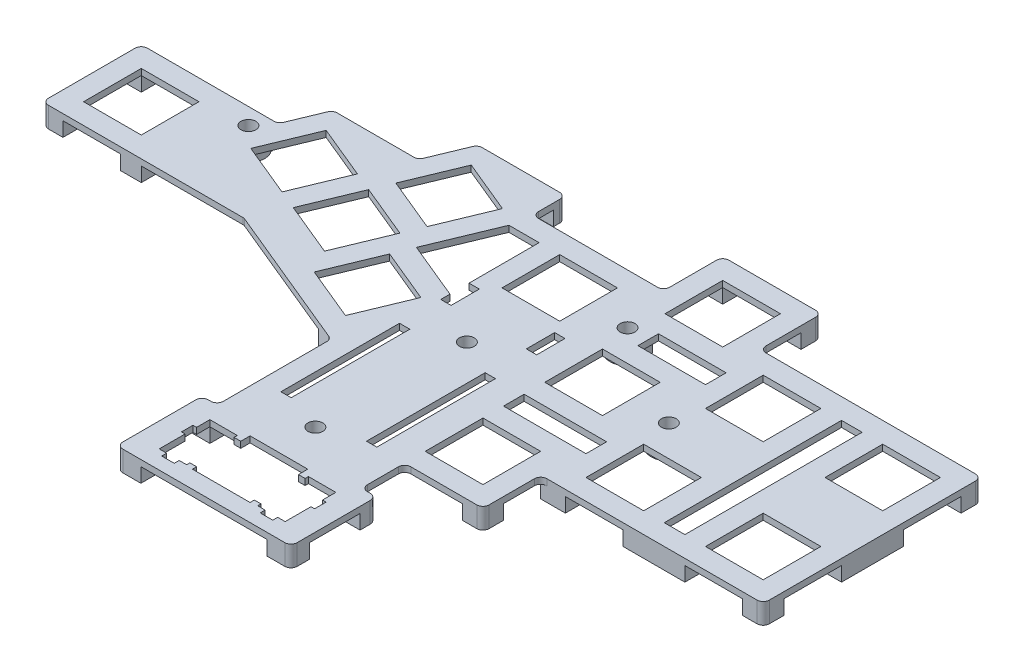
SolidWorks part; units mm, degrees
ref_plane "Front Plane" through (0, 0, 0) normal (0, 0, 1) x (1, 0, 0)
ref_plane "Top Plane" through (0, 0, 0) normal (0, 1, 0) x (1, 0, 0)
ref_plane "Right Plane" through (0, 0, 0) normal (1, 0, 0) x (0, 0, -1)
sketch "Button Reference" plane through (0, 0, 0) normal (0, 1, 0) x (1, 0, 0)
  line L0 (24.5, 61) -> (24.5, 32) construction
  line L1 (-36.2591, 48.1292) -> (-29.3708, 64.7591) construction
  line L2 (49.5, 75) -> (49.5, 46) construction
  line L3 (78.5, 75) -> (78.5, 46) construction
  line L4 (17.5, 0) -> (-17.5, 0) construction
  line L5 (-36.2591, 48.1292) -> (-19.6292, 41.2409) construction
  line L6 (17.5, -12.5) -> (-17.5, -12.5)
  line L7 (17.5, 12.5) -> (-17.5, 12.5)
  line L8 (24.6803, 89.9994) -> (49.5, 75) construction
  line L9 (24.6803, 89.9994) -> (24.5, 61) construction
  line L10 (-0.5241, 75.6559) -> (24.6803, 89.9994) construction
  line L11 (-0.5241, 75.6559) -> (24.5, 61) construction
  line L12 (-29.3708, 64.7591) -> (-12.7409, 57.8708) construction
  line L13 (-19.6292, 41.2409) -> (-12.7409, 57.8708) construction
  line L14 (-36.2591, 48.1292) -> (-12.7409, 57.8708) construction
  line L15 (-29.3708, 64.7591) -> (-19.6292, 41.2409) construction
  line L16 (-35.6984, 52.2266) -> (-28.8101, 68.8564) construction
  line L17 (-35.6984, 52.2266) -> (-52.3282, 59.1149) construction
  line L18 (-28.8101, 68.8564) -> (-45.4399, 75.7447) construction
  line L19 (-52.3282, 59.1149) -> (-45.4399, 75.7447) construction
  line L20 (-35.6984, 52.2266) -> (-45.4399, 75.7447) construction
  line L21 (-28.8101, 68.8564) -> (-52.3282, 59.1149) construction
  line L22 (-69.9281, 66.405) -> (-63.0398, 83.0348) construction
  line L23 (-69.9281, 66.405) -> (-53.2983, 59.5167) construction
  line L24 (-63.0398, 83.0348) -> (-46.41, 76.1465) construction
  line L25 (-53.2983, 59.5167) -> (-46.41, 76.1465) construction
  line L26 (-69.9281, 66.405) -> (-46.41, 76.1465) construction
  line L27 (-63.0398, 83.0348) -> (-53.2983, 59.5167) construction
  line L28 (-40.5692, 63.9856) -> (-22.9693, 56.6955) construction
  line L29 (-40.5692, 63.9856) -> (-58.1691, 71.2758) construction
  line L30 (-45.0381, 76.7148) -> (-38.1498, 93.3446) construction
  line L31 (-45.0381, 76.7148) -> (-28.4083, 69.8265) construction
  line L32 (-38.1498, 93.3446) -> (-21.52, 86.4563) construction
  line L33 (-28.4083, 69.8265) -> (-21.52, 86.4563) construction
  line L34 (-45.0381, 76.7148) -> (-21.52, 86.4563) construction
  line L35 (-38.1498, 93.3446) -> (-28.4083, 69.8265) construction
  line L36 (-40.5692, 63.9856) -> (-33.2791, 81.5855) construction
  line L37 (-24.5, 53) -> (-22.9693, 56.6955) construction
  line L38 (-58.1691, 71.2758) -> (-65.4592, 53.6759) construction
  line L39 (-65.4592, 53.6759) -> (-90.4039, 64.0083) construction
  line L40 (-70.5814, 66.1344) -> (-63.3104, 83.6881)
  line L41 (-63.3104, 83.6881) -> (-45.7105, 76.398)
  line L42 (-45.7105, 76.398) -> (-38.4204, 93.9979)
  line L43 (-38.4204, 93.9979) -> (-20.8667, 86.7269)
  line L44 (-20.8667, 86.7269) -> (-29.6876, 65.4315)
  line L45 (-29.6876, 65.4315) -> (-12.0877, 58.1414)
  line L46 (-12.0877, 58.1414) -> (-19.3586, 40.5877)
  line L47 (-19.3586, 40.5877) -> (-36.9123, 47.8586)
  line L48 (-36.9123, 47.8586) -> (-35.3816, 51.5542)
  line L49 (-35.3816, 51.5542) -> (-70.5814, 66.1344)
  line L50 (-66.484, 74.7199) -> (-66.9459, 74.9112) construction
  line L51 (-29.6436, 90.3624) -> (-29.8349, 89.9005) construction
  line L52 (-16.1851, 49.5558) -> (-15.7231, 49.3645) construction
  line L53 (-33.2791, 81.8539) -> (-33.2791, 81.5855) construction
  line L54 (46.566, 100.92) -> (46.566, 75) construction
  line L55 (46.566, 75) -> (49.5, 75) construction
  circle A0 centre (24.5, 32) radius 12.5
  circle A1 centre (24.5, 61) radius 12.5
  circle A2 centre (49.5, 46) radius 12.5
  circle A3 centre (49.5, 75) radius 12.5
  circle A4 centre (78.5, 75) radius 12.5
  circle A5 centre (78.5, 46) radius 12.5
  arc A6 (17.5, -12.5) -> (17.5, 12.5) centre (17.5, 0) ccw
  arc A7 (-17.5, 12.5) -> (-17.5, -12.5) centre (-17.5, 0) ccw
  circle A8 centre (-90.4039, 64.0083) radius 15.5
  circle A9 centre (24.6803, 89.9994) radius 12.5
  circle A10 centre (-0.5241, 75.6559) radius 12.5
  circle A11 centre (46.566, 100.92) radius 2.8
  circle A12 centre (62.066, 100.92) radius 2.8
  circle A13 centre (77.566, 100.92) radius 2.8
  circle A14 centre (93.066, 100.92) radius 2.8
  point P1 (-24.5, 53)
  point P3 (-40.5692, 63.9856)
  point P4 (-58.1691, 71.2758)
  point P35 (0, 0)
  point P43 (-33.2791, 81.5855)
  point P50 (-30, 0)
  point P51 (30, 0)
  dimension "D2" = 25
  dimension "D6" = 12.5
  dimension "D10" = 31
  dimension "D26" = 5.6
  dimension "D1" = 29
  dimension "D3" = 25
  dimension "D4" = 29
  dimension "D5" = 14
  dimension "D7" = 32
  dimension "D8" = 7
  dimension "D9" = 60
  dimension "D11" = 29
  dimension "D12" = 29
  dimension "D13" = 7
  dimension "D14" = 18
  dimension "D15" = 27
  dimension "D16" = 19.05
  dimension "D17" = 19.05
  dimension "D18" = 53
  dimension "D19" = 4
  dimension "D20" = 0.5
  dimension "D21" = 0.5
  dimension "D22" = 0.5
  dimension "D23" = 0.5
  dimension "D24" = 0.5
  dimension "D25" = 22.5
  dimension "D27" = 15.5
  dimension "D28" = 15.5
  dimension "D29" = 15.5
  dimension "D30" = 25.92
  dimension "D31" = 2.934
sketch "Sketch2" plane through (0, 0, 0) normal (0, 1, 0) x (1, 0, 0)
  line L0 (90.5, 34) -> (90.5, 87)
  line L1 (-97.4039, 57.0083) -> (-83.4039, 57.0083)
  line L2 (-97.4039, 57.0083) -> (-97.4039, 71.0083)
  line L3 (-97.4039, 71.0083) -> (-83.4039, 71.0083)
  line L4 (-83.4039, 57.0083) -> (-83.4039, 71.0083)
  line L5 (-97.4039, 57.0083) -> (-83.4039, 71.0083) construction
  line L6 (-97.4039, 71.0083) -> (-83.4039, 57.0083) construction
  line L11 (-67.315, 67.4874) -> (-61.9574, 80.4217)
  line L12 (-67.315, 67.4874) -> (-54.3807, 62.1298)
  line L17 (-61.9574, 80.4217) -> (-49.0231, 75.0641)
  line L18 (-54.3807, 62.1298) -> (-49.0231, 75.0641)
  line L23 (-67.315, 67.4874) -> (-49.0231, 75.0641) construction
  line L24 (-61.9574, 80.4217) -> (-54.3807, 62.1298) construction
  line L30 (-31.4232, 67.774) -> (-44.3575, 73.1316)
  line L31 (-31.4232, 67.774) -> (-36.7808, 54.8397)
  line L33 (-7.5241, 68.6559) -> (6.4759, 68.6559)
  line L34 (-7.5241, 68.6559) -> (-7.5241, 82.6559)
  line L35 (-7.5241, 82.6559) -> (6.4759, 82.6559)
  line L36 (6.4759, 68.6559) -> (6.4759, 82.6559)
  line L37 (-7.5241, 68.6559) -> (6.4759, 82.6559) construction
  line L38 (-7.5241, 82.6559) -> (6.4759, 68.6559) construction
  line L39 (17.6803, 82.9994) -> (31.6803, 82.9994)
  line L40 (17.6803, 82.9994) -> (17.6803, 96.9994)
  line L41 (17.6803, 96.9994) -> (31.6803, 96.9994)
  line L42 (31.6803, 82.9994) -> (31.6803, 96.9994)
  line L43 (17.6803, 82.9994) -> (31.6803, 96.9994) construction
  line L44 (17.6803, 96.9994) -> (31.6803, 82.9994) construction
  line L45 (17.5, 68) -> (31.5, 68)
  line L46 (17.5, 68) -> (17.5, 54)
  line L47 (17.5, 54) -> (31.5, 54)
  line L48 (31.5, 68) -> (31.5, 54)
  line L49 (17.5, 68) -> (31.5, 54) construction
  line L50 (17.5, 54) -> (31.5, 68) construction
  line L51 (17.5, 39) -> (31.5, 39)
  line L52 (17.5, 39) -> (17.5, 25)
  line L53 (17.5, 25) -> (31.5, 25)
  line L54 (31.5, 39) -> (31.5, 25)
  line L55 (17.5, 39) -> (31.5, 25) construction
  line L56 (17.5, 25) -> (31.5, 39) construction
  line L57 (42.5, 39) -> (56.5, 39)
  line L58 (42.5, 39) -> (42.5, 53)
  line L59 (42.5, 53) -> (56.5, 53)
  line L60 (56.5, 39) -> (56.5, 53)
  line L61 (42.5, 39) -> (56.5, 53) construction
  line L62 (42.5, 53) -> (56.5, 39) construction
  line L63 (42.5, 82) -> (56.5, 82)
  line L64 (42.5, 82) -> (42.5, 68)
  line L65 (42.5, 68) -> (56.5, 68)
  line L66 (56.5, 82) -> (56.5, 68)
  line L67 (42.5, 82) -> (56.5, 68) construction
  line L68 (42.5, 68) -> (56.5, 82) construction
  line L69 (71.5, 68) -> (85.5, 68)
  line L70 (71.5, 68) -> (71.5, 82)
  line L71 (71.5, 82) -> (85.5, 82)
  line L72 (85.5, 68) -> (85.5, 82)
  line L73 (71.5, 68) -> (85.5, 82) construction
  line L74 (71.5, 82) -> (85.5, 68) construction
  line L75 (71.5, 39) -> (85.5, 39)
  line L76 (71.5, 39) -> (71.5, 53)
  line L77 (71.5, 53) -> (85.5, 53)
  line L78 (85.5, 39) -> (85.5, 53)
  line L79 (71.5, 39) -> (85.5, 53) construction
  line L80 (71.5, 53) -> (85.5, 39) construction
  line L85 (7, 4.73) -> (8.6226, 4.73)
  line L88 (-44.3575, 73.1316) -> (-49.7151, 60.1973)
  line L89 (-36.7808, 54.8397) -> (-49.7151, 60.1973)
  line L90 (-31.4232, 67.774) -> (-49.7151, 60.1973) construction
  line L91 (-44.3575, 73.1316) -> (-36.7808, 54.8397) construction
  line L92 (-33.6459, 49.2116) -> (-20.7116, 43.8541)
  line L93 (-33.6459, 49.2116) -> (-28.2884, 62.1459)
  line L94 (-20.7116, 43.8541) -> (-15.3541, 56.7884)
  line L95 (-28.2884, 62.1459) -> (-15.3541, 56.7884)
  line L96 (-33.6459, 49.2116) -> (-15.3541, 56.7884) construction
  line L97 (-20.7116, 43.8541) -> (-28.2884, 62.1459) construction
  line L98 (-42.425, 77.7972) -> (-37.0674, 90.7315)
  line L99 (-42.425, 77.7972) -> (-29.4907, 72.4396)
  line L100 (-37.0674, 90.7315) -> (-24.1331, 85.3739)
  line L101 (-29.4907, 72.4396) -> (-24.1331, 85.3739)
  line L102 (-42.425, 77.7972) -> (-24.1331, 85.3739) construction
  line L103 (-37.0674, 90.7315) -> (-29.4907, 72.4396) construction
  line L104 (-28.8101, 68.8564) -> (-45.4399, 75.7447) construction
  line L106 (90.5, 87) -> (36.6803, 87)
  line L107 (36.6803, 87) -> (36.6803, 101.9994)
  line L128 (21.1524, -11.22) -> (-21.1524, -11.22)
  line L129 (-102.4039, 76.0083) -> (-102.4039, 52.0083)
  line L131 (90.5, 34) -> (36.5, 34)
  line L132 (36.5, 34) -> (36.5, 20)
  line L133 (36.5, 20) -> (17.5, 20)
  line L134 (17.5, 20) -> (17.5, 9.5)
  line L137 (36.6803, 101.9994) -> (12.6803, 101.9994)
  line L138 (-40.4083, 95.7315) -> (-44.6788, 85.4217)
  line L139 (-44.6788, 85.4217) -> (-65.2983, 85.4217)
  line L140 (-65.2983, 85.4217) -> (-69.1975, 76.0083)
  line L141 (-69.1975, 76.0083) -> (-102.4039, 76.0083)
  line L142 (-17.5, 9.5) -> (-17.5, 37.1118)
  line L143 (-17.5, 37.1118) -> (-53.4633, 52.0083)
  line L144 (-53.4633, 52.0083) -> (-102.4039, 52.0083)
  line L145 (-40.4083, 95.7315) -> (-19.1331, 95.7315)
  line L146 (12.6803, 87.6559) -> (12.6803, 101.9994)
  line L150 (-17.5, 9.5) -> (-21.1524, 9.5)
  line L151 (-21.1524, -11.22) -> (-21.1524, 9.5)
  line L154 (17.5, 9.5) -> (21.1524, 9.5)
  line L155 (21.1524, -11.22) -> (21.1524, 9.5)
  line L171 (-7, 7) -> (7, 7)
  line L174 (7, -7) -> (7, -5.97)
  line L175 (17.5, 9.5) -> (-17.5, 9.5) construction
  line L176 (0, 7) -> (0, -7) construction
  line L185 (-7, -7) -> (7, -7)
  line L186 (8.6226, 4.73) -> (8.6226, 5.53)
  line L187 (8.6226, 5.53) -> (15.2774, 5.53)
  line L188 (15.2774, 5.53) -> (15.2774, 2.3)
  line L189 (15.2774, 2.3) -> (16.1524, 2.3)
  line L190 (16.1524, 2.3) -> (16.1524, -0.5)
  line L191 (16.1524, -0.5) -> (15.2774, -0.5)
  line L192 (15.2774, -0.5) -> (15.2774, -6.77)
  line L193 (15.2774, -6.77) -> (13.474, -6.77)
  line L194 (13.474, -6.77) -> (13.474, -7.97)
  line L195 (13.474, -7.97) -> (10.426, -7.97)
  line L196 (10.426, -7.97) -> (10.426, -6.77)
  line L197 (10.426, -6.77) -> (8.6226, -6.77)
  line L198 (8.6226, -6.77) -> (8.6226, -5.97)
  line L199 (8.6226, -5.97) -> (7, -5.97)
  line L200 (11.95, 5.53) -> (11.95, -7.97) construction
  line L201 (-16.1524, 0) -> (16.1524, 0) construction
  line L202 (7, 4.73) -> (7, 7)
  line L203 (-8.6226, 4.73) -> (-8.6226, 5.53)
  line L204 (-8.6226, -6.77) -> (-8.6226, -5.97)
  line L205 (-7, -7) -> (-7, -5.97)
  line L206 (-8.6226, -5.97) -> (-7, -5.97)
  line L207 (-10.426, -6.77) -> (-8.6226, -6.77)
  line L208 (-10.426, -7.97) -> (-10.426, -6.77)
  line L209 (-13.474, -6.77) -> (-13.474, -7.97)
  line L210 (-13.474, -7.97) -> (-10.426, -7.97)
  line L211 (-11.95, 5.53) -> (-11.95, -7.97) construction
  line L212 (-15.2774, -6.77) -> (-13.474, -6.77)
  line L213 (-15.2774, -0.5) -> (-15.2774, -6.77)
  line L214 (-16.1524, -0.5) -> (-15.2774, -0.5)
  line L215 (-16.1524, 2.3) -> (-16.1524, -0.5)
  line L216 (-15.2774, 2.3) -> (-16.1524, 2.3)
  line L217 (-15.2774, 5.53) -> (-15.2774, 2.3)
  line L218 (-8.6226, 5.53) -> (-15.2774, 5.53)
  line L219 (-7, 4.73) -> (-8.6226, 4.73)
  line L220 (-7, 4.73) -> (-7, 7)
  line L222 (12.6803, 87.6559) -> (-19.1331, 87.6559)
  line L223 (-19.1331, 87.6559) -> (-19.1331, 95.7315)
  point P0 (-90.4039, 64.0083)
  point P6 (12.05, 5.1416)
  point P7 (-58.1691, 71.2758)
  point P8 (-40.5692, 63.9856)
  point P9 (-24.5, 53)
  point P15 (-33.2791, 81.5855)
  point P17 (0, 0)
  point P31 (-11.95, -7.97)
  point P32 (-0.5241, 75.6559)
  point P38 (24.6803, 89.9994)
  point P44 (24.5, 61)
  point P50 (24.5, 32)
  point P56 (49.5, 46)
  point P62 (49.5, 75)
  point P68 (78.5, 75)
  point P74 (78.5, 46)
  point P80 (0, 0)
  point P81 (0, 0)
  point P86 (0, 0)
  point P87 (0, 0)
  point P91 (0, 0)
  point P93 (0, 0)
  point P94 (12.6803, 99.1435)
  point P95 (0, 0)
  point P159 (0, 9.5)
  point P174 (0, 0)
  dimension "D2" = 5
  dimension "D3" = 14
  dimension "D5" = 5
  dimension "D6" = 5
  dimension "D7" = 5
  dimension "D8" = 5
  dimension "D9" = 5
  dimension "D10" = 6.6548
  dimension "D11" = 5
  dimension "D12" = 5
  dimension "D13" = 5
  dimension "D14" = 5
  dimension "D15" = 5
  dimension "D16" = 5
  dimension "D17" = 35
  dimension "D18" = 5
  dimension "D19" = 5
  dimension "D20" = 3.048
  dimension "D21" = 5
  dimension "D22" = 5
  dimension "D23" = 14
  dimension "D24" = 0.875
  dimension "D25" = 14
  dimension "D27" = 4.73
  dimension "D28" = 2.3
  dimension "D29" = 0.5
  dimension "D30" = 7.97
  dimension "D31" = 6.77
  dimension "D32" = 5.97
  dimension "D33" = 23.9
  dimension "D26" = 5.53
  dimension "D36" = 5
  dimension "D37" = 5
  dimension "D38" = 2.5
  dimension "D39" = 3.25
  dimension "D40" = 5
  dimension "D41" = 5
extrude "Key Plate" add sketch "Sketch2" along normal blind 1.5
sketch "Sketch3" plane through (0, 0, 0) normal (0, -1, 0) x (1, 0, 0)
  line L0 (-20.7116, -43.8541) -> (-22.625, -39.2347)
  line L13 (90.5, -34) -> (85.5, -34)
  line L14 (90.5, -34) -> (90.5, -39)
  line L15 (90.5, -39) -> (85.5, -39)
  line L16 (85.5, -34) -> (85.5, -39)
  line L17 (36.5, -20) -> (31.5, -20)
  line L18 (36.5, -20) -> (36.5, -25)
  line L19 (36.5, -25) -> (31.5, -25)
  line L20 (31.5, -20) -> (31.5, -25)
  line L29 (-102.4039, -52.0083) -> (-97.4039, -52.0083)
  line L30 (-102.4039, -52.0083) -> (-102.4039, -57.0083)
  line L31 (-102.4039, -57.0083) -> (-97.4039, -57.0083)
  line L32 (-97.4039, -52.0083) -> (-97.4039, -57.0083)
  line L33 (-97.4039, -71.0083) -> (-102.4039, -71.0083)
  line L34 (-97.4039, -71.0083) -> (-97.4039, -76.0083)
  line L35 (-97.4039, -76.0083) -> (-102.4039, -76.0083)
  line L36 (-102.4039, -71.0083) -> (-102.4039, -76.0083)
  line L37 (-20.7116, -43.8541) -> (-16.0922, -41.9406)
  line L38 (-22.625, -39.2347) -> (-18.0056, -37.3212)
  line L40 (-53.4633, -52.0083) -> (-17.5, -37.1118) construction
  line L49 (-16.0922, -41.9406) -> (-18.0056, -37.3212)
  line L51 (-102.4039, -52.0083) -> (-53.4633, -52.0083) construction
  line L52 (-83.4039, -57.0083) -> (-78.4039, -57.0083)
  line L53 (-83.4039, -57.0083) -> (-83.4039, -52.0083)
  line L54 (-83.4039, -52.0083) -> (-78.4039, -52.0083)
  line L55 (-78.4039, -57.0083) -> (-78.4039, -52.0083)
  line L56 (-38.4204, -93.9979) -> (-20.8667, -86.7269) construction
  line L57 (17.6803, -96.9994) -> (12.6803, -96.9994)
  line L58 (36.5, -34) -> (90.5, -34) construction
  line L59 (-83.4039, -71.0083) -> (-76.2052, -71.0083)
  line L60 (-83.4039, -71.0083) -> (-83.4039, -76.0083)
  line L61 (-83.4039, -76.0083) -> (-69.1975, -76.0083)
  line L62 (-69.1975, -74.2697) -> (-69.1975, -76.0083)
  line L71 (36.5, -34) -> (42.5, -34)
  line L72 (36.5, -34) -> (36.5, -39)
  line L73 (36.5, -39) -> (42.5, -39)
  line L74 (42.5, -34) -> (42.5, -39)
  line L75 (56.5, -39) -> (71.5, -39)
  line L76 (56.5, -39) -> (56.5, -34)
  line L77 (56.5, -34) -> (71.5, -34)
  line L78 (71.5, -39) -> (71.5, -34)
  line L79 (90.5, -34) -> (90.5, -87) construction
  line L80 (85.5, -53) -> (90.5, -53)
  line L81 (85.5, -53) -> (85.5, -68)
  line L82 (85.5, -68) -> (90.5, -68)
  line L83 (90.5, -53) -> (90.5, -68)
  line L85 (36.6803, -101.9994) -> (31.6803, -101.9994)
  line L86 (36.6803, -101.9994) -> (36.6803, -96.9994)
  line L87 (36.6803, -96.9994) -> (31.6803, -96.9994)
  line L88 (31.6803, -101.9994) -> (31.6803, -96.9994)
  line L89 (85.5, -82) -> (90.5, -82)
  line L90 (85.5, -82) -> (85.5, -87)
  line L91 (85.5, -87) -> (90.5, -87)
  line L92 (90.5, -82) -> (90.5, -87)
  line L95 (-70.5814, -66.1344) -> (-63.3104, -83.6881) construction
  line L96 (17.5, -12.5) -> (-17.5, -12.5) construction
  line L97 (17.6803, -96.9994) -> (17.6803, -101.9994)
  line L98 (17.6803, -101.9994) -> (12.6803, -101.9994)
  line L99 (12.6803, -96.9994) -> (12.6803, -101.9994)
  line L100 (-19.1331, -95.7315) -> (-35.363, -95.7315)
  line L101 (-19.1331, -95.7315) -> (-19.1331, -92.7315)
  line L102 (-19.1331, -92.7315) -> (-35.363, -92.7315)
  line L103 (-35.363, -95.7315) -> (-35.363, -92.7315)
  line L105 (21.1524, 11.22) -> (15.2774, 11.22)
  line L106 (21.1524, 11.22) -> (21.1524, 6.77)
  line L107 (21.1524, 6.77) -> (15.2774, 6.77)
  line L108 (15.2774, 11.22) -> (15.2774, 6.77)
  line L109 (-21.1524, 11.22) -> (-15.2774, 11.22)
  line L110 (-21.1524, 11.22) -> (-21.1524, 6.77)
  line L111 (-21.1524, 6.77) -> (-15.2774, 6.77)
  line L112 (-15.2774, 11.22) -> (-15.2774, 6.77)
  line L113 (21.1524, -9.5) -> (15.2774, -9.5)
  line L114 (21.1524, -9.5) -> (21.1524, -5.53)
  line L115 (21.1524, -5.53) -> (15.2774, -5.53)
  line L116 (15.2774, -9.5) -> (15.2774, -5.53)
  line L117 (-21.1524, -9.5) -> (-15.2774, -9.5)
  line L118 (-21.1524, -9.5) -> (-21.1524, -5.53)
  line L119 (-21.1524, -5.53) -> (-15.2774, -5.53)
  line L120 (-15.2774, -9.5) -> (-15.2774, -5.53)
  circle A0 centre (-0.4039, -53) radius 4.25
  circle A1 centre (-0.9039, -16.75) radius 4.25
  circle A2 centre (41.0961, -60.5) radius 4.2594
  circle A3 centre (16.0961, -75.5) radius 4.2594
  arc A4 (-69.1975, -74.2697) -> (-76.2052, -71.0083) centre (-72.4039, -72) ccw
  circle A5 centre (24.5, -61) radius 12.5 construction
  circle A6 centre (49.5, -46) radius 12.5 construction
  point P0 (41.0961, -60.5)
  dimension "D1" = 8.5
  dimension "D2" = 3
  dimension "D3" = 5
extrude "Feet" add sketch "Sketch3" along normal blind 3.5
hole_wizard "M3 Clearance Hole1" positions "3DSketch1" profile "Sketch5" hole size "M3" standard "ANSI Metric" end condition up to next
sketch3d "3DSketch1"
  line L0 (-0.4039, -3.5, -53) -> (-0.4039, 0, -53) construction
  line L1 (16.0961, -3.5, -75.5) -> (16.0961, 0, -75.5) construction
  line L2 (-0.9039, -3.5, -16.75) -> (-0.9039, 0, -16.75) construction
  line L3 (41.0961, -3.5, -60.5) -> (41.0961, 0, -60.5) construction
  line L4 (-72.4039, -3.5, -72) -> (-72.4039, 0, -72) construction
  point P0 (-0.4039, -3.5, -53)
  point P4 (41.0961, -3.5, -60.5)
  point P6 (16.0961, -3.5, -75.5)
  point P10 (-0.9039, -3.5, -16.75)
  point P18 (-72.4039, -3.5, -72)
sketch "Sketch5" plane through (-0.4039, -3.5, -53) normal (1, 0, 0) x (0, 0, -1)
  line L0 (0, 0) -> (0, 5)
  line L1 (0, 5) -> (1.8, 5)
  line L2 (1.8, 5) -> (1.8, 0.025)
  line L3 (1.8, 0.025) -> (1.825, 0)
  line L5 (1.825, 0) -> (0, 0)
  line L6 (-1.8, 0.025) -> (-1.825, 0) construction
  line L11 (0, -6.35) -> (0, 107.95) construction
  dimension "Thru Hole Dia." = 3.6
  dimension "Thru Hole Depth" = 5
  dimension "Near C'Sink Dia." = 3.65
  dimension "Near C'Sink Angle" = 90
fillet "Fillet1" radius 1.5 25 edges at (-21.1524, -1, 11.22) (-21.1524, -1, -9.5) (-17.5, 0.75, -9.5) (-17.5, 0.75, -37.1118) (-53.4633, 0.75, -52.0083) (-102.4039, -1, -52.0083) (-102.4039, -1, -76.0083) (-69.1975, 0.75, -76.0083) (-65.2983, 0.75, -85.4217) (-44.6788, 0.75, -85.4217) (-40.4083, 0.75, -95.7315) (-19.1331, -1, -95.7315) (-19.1331, 0.75, -87.6559) (12.6803, 0.75, -87.6559) (12.6803, -1, -101.9994) (90.5, -1, -34) (36.5, 0.75, -34) (36.5, -1, -20) (17.5, 0.75, -20) (17.5, 0.75, -9.5) (21.1524, -1, -9.5) (21.1524, -1, 11.22) (36.6803, -1, -101.9994) (36.6803, 0.75, -87) (90.5, -1, -87)
sketch "Sketch6" plane through (0, 0, 0) normal (0, -1, 0) x (-1, 0, 0)
  line L0 (12.5241, 58.7884) -> (10.0241, 58.7884)
  line L5 (-10.75, 65.6559) -> (-8.25, 65.6559)
  line L6 (-10.75, 65.6559) -> (-10.75, 58.7884)
  line L7 (-56.5, 39) -> (-56.5, 53) construction
  line L8 (-61.5, 39) -> (-66.5, 39)
  line L9 (-61.5, 39) -> (-61.5, 82)
  line L10 (-61.5, 82) -> (-66.5, 82)
  line L11 (-66.5, 39) -> (-66.5, 82)
  line L12 (-71.5, 53) -> (-71.5, 39) construction
  line L13 (-71.5, 34) -> (-56.5, 34) construction
  line L14 (-85.5, 87) -> (-38.1803, 87) construction
  line L15 (12.5241, 61.0281) -> (26.4211, 66.7845)
  line L16 (26.4211, 66.7845) -> (19.847, 82.6559)
  line L17 (19.847, 82.6559) -> (12.5241, 82.6559)
  line L18 (12.5241, 82.6559) -> (12.5241, 65.6559)
  line L19 (15.3541, 56.7884) -> (28.2884, 62.1459) construction
  line L20 (29.4907, 72.4396) -> (24.1331, 85.3739) construction
  line L21 (-11.1803, 87.6559) -> (17.6331, 87.6559) construction
  line L22 (7.5241, 82.6559) -> (7.5241, 68.6559) construction
  line L23 (-42.5, 53) -> (-42.5, 39) construction
  line L24 (-37.5, 49) -> (-17.5, 49)
  line L25 (-37.5, 49) -> (-37.5, 44)
  line L26 (-37.5, 44) -> (-17.5, 44)
  line L27 (-17.5, 49) -> (-17.5, 44)
  line L28 (-17.5, 54) -> (-31.5, 54) construction
  line L29 (-31.5, 39) -> (-17.5, 39) construction
  line L30 (-42.5, 82) -> (-42.5, 68) construction
  line L31 (-37.5, 77.9994) -> (-21.0961, 77.9994)
  line L32 (-37.5, 77.9994) -> (-37.5, 73)
  line L33 (-37.5, 73) -> (-21.0961, 73)
  line L34 (-21.0961, 77.9994) -> (-21.0961, 73)
  line L35 (-17.6803, 82.9994) -> (-31.6803, 82.9994) construction
  line L36 (-31.5, 68) -> (-17.5, 68) construction
  line L37 (-10.75, 20) -> (-8.25, 20)
  line L38 (-8.25, 65.6559) -> (-8.25, 58.7884)
  line L39 (12.5241, 20) -> (10.0241, 20)
  line L40 (12.5241, 20) -> (12.5241, 48.7884)
  line L41 (12.5241, 65.6559) -> (10.0241, 65.6559)
  line L42 (10.0241, 20) -> (10.0241, 48.7884)
  line L43 (-17.5, 25) -> (-31.5, 25) construction
  line L44 (7.5241, 68.6559) -> (-6.4759, 68.6559) construction
  line L45 (12.5241, 48.7884) -> (10.0241, 48.7884)
  line L46 (-8.25, 58.7884) -> (-10.75, 58.7884)
  line L47 (-8.25, 48.7884) -> (-10.75, 48.7884)
  line L48 (-8.25, 48.7884) -> (-8.25, 20)
  line L49 (-10.75, 48.7884) -> (-10.75, 20)
  line L50 (12.5241, 58.7884) -> (12.5241, 61.0281)
  line L51 (10.0241, 58.7884) -> (10.0241, 65.6559)
  circle A2 centre (-16.0961, 75.5) radius 4.2594 construction
  point P66 (12.5241, 57.4416)
  dimension "D3" = 2.5
  dimension "D4" = 20
  dimension "D5" = 5
  dimension "D6" = 5
  dimension "D7" = 5
  dimension "D8" = 5
  dimension "D9" = 5
  dimension "D10" = 5
  dimension "D11" = 5
  dimension "D12" = 5
  dimension "D13" = 5
  dimension "D14" = 5
  dimension "D15" = 5
  dimension "D16" = 6.75
  dimension "D17" = 5
  dimension "D18" = 5
  dimension "D19" = 5
  dimension "D20" = 5
  dimension "D21" = 5
  dimension "D22" = 3
  dimension "D23" = 8
  dimension "D24" = 2
extrude "Cut-Extrude1" cut sketch "Sketch6" against normal blind 10
sketch "Sketch7" plane through (0, 1.5, 0) normal (0, 1, 0) x (1, 0, 0)
  line L1 (-119.9237, 112.9004) -> (105.3648, 112.9004)
  line L2 (-119.9237, 112.9004) -> (-119.9237, 10.3069)
  line L3 (-119.9237, 10.3069) -> (105.3648, 10.3069)
  line L4 (105.3648, 112.9004) -> (105.3648, 10.3069)
extrude "Cut-Extrude2" [suppressed] cut sketch "Sketch7" against normal blind 10
